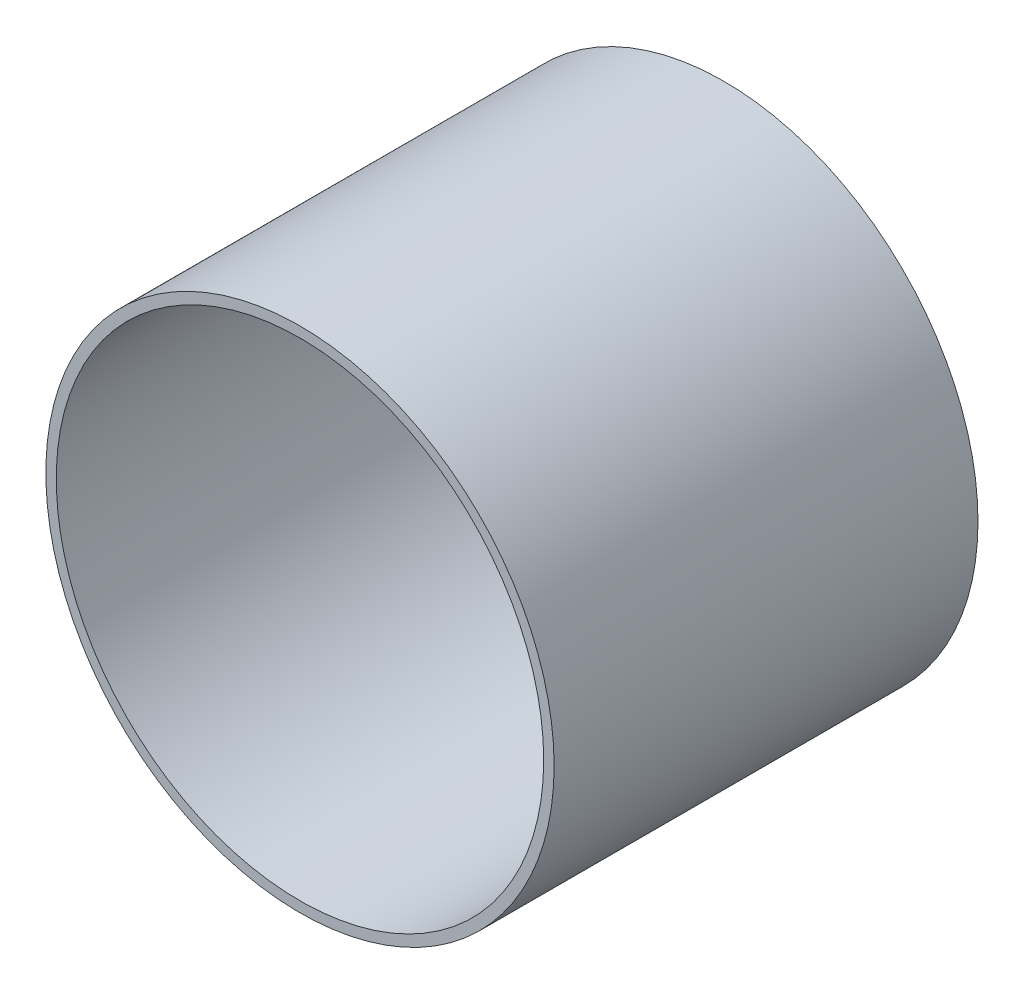
SolidWorks part; units mm, degrees
ref_plane "Front Plane" through (0, 0, 0) normal (0, 0, 1) x (1, 0, 0)
ref_plane "Top Plane" through (0, 0, 0) normal (0, 1, 0) x (1, 0, 0)
ref_plane "Right Plane" through (0, 0, 0) normal (1, 0, 0) x (0, 0, -1)
sketch "Sketch1" plane through (0, 0, 0) normal (0, 0, 1) x (1, 0, 0)
  circle A0 centre (0, 0) radius 38.0746
  circle A1 centre (0, 0) radius 36.5125
  dimension "D1" = 73.025
  dimension "D2" = 76.1492
extrude "Boss-Extrude1" add sketch "Sketch1" along normal mid plane 63.5
equation "\"AIRFRAME_OD\"= 3.091in"
equation "\"AIRFRAME_ID\"= 3.00in"
equation "\"FLAT_T\"= 0.125in"
equation "\"NOSE_EXP_L\"= 3.5in"
equation "\"NOSE_SHOULDER_L\"= 5in"
equation "\"MAIN_L\"= 30in"
equation "\"RECO_COUP_L\"= 6in"
equation "\"RECO_SWITCH_L\"= 1.5in"
equation "\"DROGUE_L\"= 14in"
equation "\"ATS_FORE_COUP_L\"= 4in"
equation "\"ATS_AFT_COUP_L\"= 2.5in"
equation "\"LOWER_L\"= 16in"
equation "\"FIN_N\"= 4"
equation "\"CR_AFT_X\"= 0.5in"
equation "\"CR_FORE_X\"= 6in"
equation "\"D1@Sketch1\"=\"COUPLER_ID\""
equation "\"D2@Sketch1\"=\"COUPLER_OD\""
equation "\"D1@Boss-Extrude1\"=\"ATS_AFT_COUP_L\""
equation "\"FIN_ROOT\"= 5in"
equation "\"FIN_X\"= 0.75in"
equation "\"MOTOR_OD\"= 2.25in"
equation "\"MOTOR_ID\"= 2.126in"
equation "\"COUPLER_OD\"= 2.998in"
equation "\"COUPLER_ID\"= 2.875in"
equation "\"RECO_ROD_X\"= 1.5in"
equation "\"ATS_ROD_X\"= 2in"
equation "\"MOTOR_L\"= 8in"
equation "\"MOTOR_LOWER_X\"= 0.5in"
